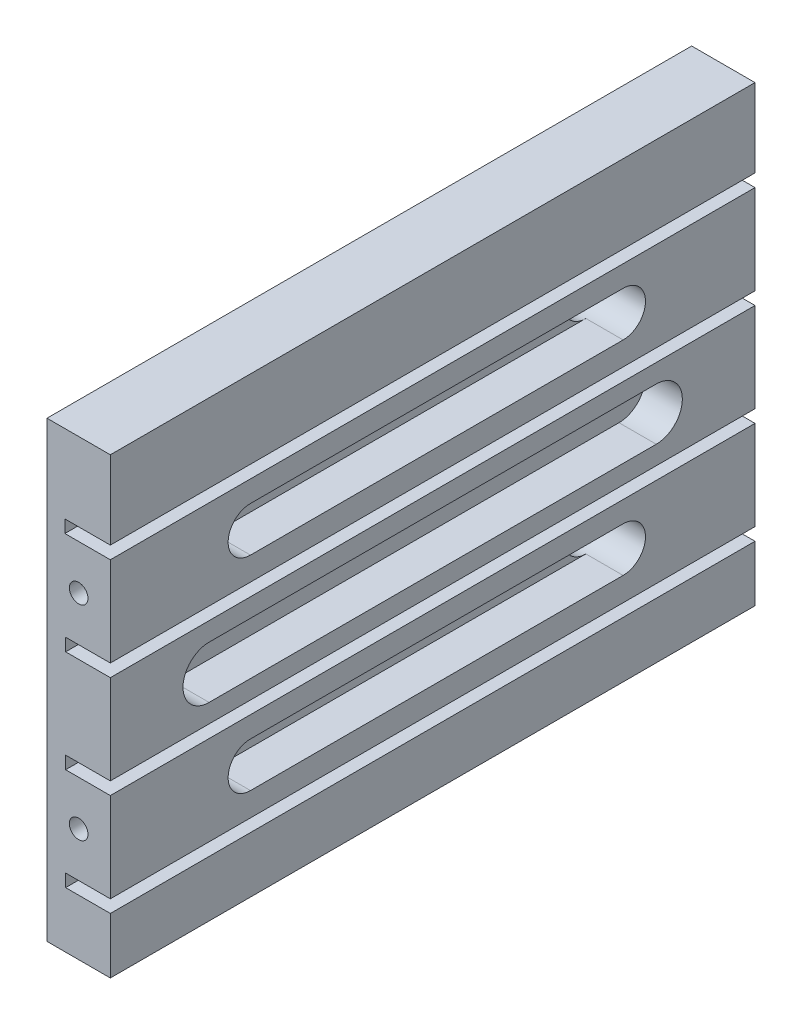
SolidWorks part; units mm, degrees
material "6061-T6 (SS)"
ref_plane "Front Plane" through (0, 0, 0) normal (0, 0, 1) x (1, 0, 0)
ref_plane "Top Plane" through (0, 0, 0) normal (0, 1, 0) x (1, 0, 0)
ref_plane "Right Plane" through (0, 0, 0) normal (1, 0, 0) x (0, 0, -1)
sketch "Sketch1" plane through (0, 0, 0) normal (0, 0, 1) x (1, 0, 0)
  line L0 (0, 0) -> (0, 60.8)
  line L1 (0, 60.8) -> (8.5, 60.8)
  line L2 (8.5, 60.8) -> (8.5, 50.3)
  line L3 (8.5, 50.3) -> (2.4, 50.3)
  line L4 (2.4, 50.3) -> (2.4, 48.6)
  line L5 (2.4, 48.6) -> (8.5, 48.6)
  line L6 (8.5, 48.6) -> (8.5, 36.6)
  line L7 (8.5, 36.6) -> (2.5, 36.6)
  line L8 (2.5, 36.6) -> (2.5, 34.9)
  line L9 (2.5, 34.9) -> (8.5, 34.9)
  line L10 (8.5, 34.9) -> (8.5, 22.9)
  line L11 (8.5, 22.9) -> (2.5, 22.9)
  line L12 (2.5, 22.9) -> (2.5, 21.2)
  line L13 (2.5, 21.2) -> (8.5, 21.2)
  line L14 (8.5, 21.2) -> (8.5, 9.2)
  line L15 (8.5, 9.2) -> (2.5, 9.2)
  line L16 (2.5, 9.2) -> (2.5, 7.5)
  line L17 (2.5, 7.5) -> (8.5, 7.5)
  line L18 (8.5, 7.5) -> (8.5, 0)
  line L19 (8.5, 0) -> (0, 0)
  dimension "D1" = 60.8
  dimension "D2" = 8.5
  dimension "D3" = 10.5
  dimension "D4" = 1.7
  dimension "D5" = 6.1
  dimension "D6" = 12
  dimension "D7" = 1.7
  dimension "D8" = 12
  dimension "D9" = 12
  dimension "D10" = 1.7
  dimension "D11" = 1.7
  dimension "D12" = 2.5
  dimension "D13" = 2.5
  dimension "D14" = 2.5
  dimension "D15" = 8.5
  dimension "D16" = 8.5
  dimension "D17" = 8.5
  dimension "D18" = 8.5
extrude "Boss-Extrude1" add sketch "Sketch1" along normal blind 86.5
sketch "Sketch2" plane through (0, 0, 86.5) normal (0, 0, 1) x (1, 0, 0)
  line L0 (8.5, 36.6) -> (8.5, 48.6) construction
  line L3 (8.5, 48.6) -> (2.4, 48.6) construction
  line L4 (8.5, 21.2) -> (2.5, 21.2) construction
  line L8 (8.5, 9.2) -> (8.5, 21.2) construction
  point P0 (4.25, 15.2)
  point P11 (4.25, 42.6)
  dimension "D1" = 4.25
  dimension "D2" = 6
  dimension "D3" = 4.25
  dimension "D4" = 6
hole_wizard "M3x0.5 Tapped Hole2" positions "Sketch3" profile "Sketch4" tap size "M3x0.5" standard "ANSI Metric"
sketch "Sketch3" plane through (0, 0, 86.5) normal (0, 0, 1) x (1, 0, 0)
  point P0 (4.25, 42.6)
  point P3 (4.25, 15.2)
sketch "Sketch4" plane through (4.25, 42.6, 86.5) normal (1, 0, 0) x (0, -1, 0)
  line L0 (0, 0) -> (0, 6.7511)
  line L1 (0, 6.7511) -> (1.25, 6)
  line L2 (1.25, 6) -> (1.25, 0)
  line L5 (1.25, 0) -> (0, 0)
  line L10 (0, 6.7511) -> (-1.25, 6) construction
  line L11 (0, -6.35) -> (0, 107.95) construction
  dimension "Tap Drill Dia." = 2.5
  dimension "Tap Drill Depth" = 6
  dimension "Drill Angle" = 118
ref_plane "Plane1" through (0, 0, 43.25) normal (0, 0, 1) x (1, 0, 0)
mirror "Mirror1" about plane through (0, 0, 43.25) normal (0, 0, 1) of "M3x0.5 Tapped Hole2"
sketch "Sketch5" plane through (0, 0, 0) normal (-1, 0, 0) x (0, 0, 1)
  line L1 (86.5, 60.8) -> (0, 60.8) construction
  line L5 (0, 60.8) -> (0, 0) construction
  line L7 (86.5, 0) -> (0, 0) construction
  line L8 (86.5, 60.8) -> (86.5, 0) construction
  point P0 (78.25, 5)
  point P3 (8.25, 5)
  point P4 (8.25, 55.8)
  point P7 (78.25, 55.8)
  dimension "D1" = 5
  dimension "D2" = 8.25
  dimension "D3" = 70
  dimension "D4" = 5
  dimension "D5" = 5
  dimension "D6" = 8.25
  dimension "D7" = 8.25
  dimension "D8" = 5
hole_wizard "M3x0.5 Tapped Hole1" positions "Sketch10" profile "Sketch11" tap size "M3x0.5" standard "ANSI Metric"
sketch "Sketch10" plane through (0, 0, 0) normal (-1, 0, 0) x (0, 0, 1)
  line L0 (43.25, 60.8) -> (43.25, 0) construction
  line L1 (86.5, 60.8) -> (0, 60.8) construction
  line L2 (86.5, 0) -> (0, 0) construction
  line L7 (43.25, 54) -> (8.25, 54) construction
  line L12 (43.25, 5) -> (8.25, 5) construction
  point P16 (8.25, 54)
  point P26 (8.25, 5)
  dimension "D1" = 49
sketch "Sketch11" plane through (0, 5, 8.25) normal (0, 1, 0) x (0, 0, 1)
  line L0 (0, 0) -> (0, 4.7511)
  line L1 (0, 4.7511) -> (1.25, 4)
  line L2 (1.25, 4) -> (1.25, 0)
  line L5 (1.25, 0) -> (0, 0)
  line L10 (0, 4.7511) -> (-1.25, 4) construction
  line L11 (0, -6.35) -> (0, 107.95) construction
  dimension "Tap Drill Dia." = 2.5
  dimension "Tap Drill Depth" = 4
  dimension "Drill Angle" = 118
ref_plane "Plane2" through (0, 0, 43.25) normal (0, 0, -1) x (-1, 0, 0)
mirror "Mirror2" about plane through (0, 0, 43.25) normal (0, 0, -1) of "M3x0.5 Tapped Hole1"
sketch "Sketch14" plane through (8.5, 0, 0) normal (1, 0, 0) x (0, 0, -1)
  line L0 (-43.25, 60.8) -> (-43.25, 0) construction
  line L1 (-86.5, 60.8) -> (0, 60.8) construction
  line L2 (-86.5, 0) -> (0, 0) construction
  line L3 (-86.5, 28.9) -> (0, 28.9) construction
  line L4 (-86.5, 22.9) -> (-86.5, 34.9) construction
  line L5 (0, 22.9) -> (0, 34.9) construction
  line L6 (-73.25, 32.4) -> (-13.25, 32.4)
  line L7 (-13.25, 25.4) -> (-73.25, 25.4)
  circle A0 centre (-73.25, 28.9) radius 3.5
  circle A1 centre (-13.25, 28.9) radius 3.5
  dimension "D1" = 7
  dimension "D2" = 30
extrude "Cut-Extrude3" cut sketch "Sketch14" against normal offset from surface (5 mm away) 5 contours A1 L6 A0 L7 | A0 | A1 up to face at (8.5, 28.9, 43.25)
sketch "Sketch12" plane through (8.5, 0, 0) normal (1, 0, 0) x (0, 0, -1)
  line L0 (-42.6954, 60.8) -> (-42.6954, 0) construction
  line L1 (-86.5, 60.8) -> (0, 60.8) construction
  line L2 (-86.5, 0) -> (0, 0) construction
  line L4 (-67.6954, 45.7404) -> (-17.6954, 45.7404)
  line L5 (-67.6954, 39.7404) -> (-17.6954, 39.7404)
  line L6 (-67.6954, 18.3789) -> (-17.6954, 18.3789)
  line L7 (-67.6954, 12.3789) -> (-17.6954, 12.3789)
  circle A0 centre (-67.6954, 42.7404) radius 3
  circle A1 centre (-17.6954, 42.7404) radius 3
  circle A2 centre (-17.6954, 15.3789) radius 3
  circle A3 centre (-67.6954, 15.3789) radius 3
  dimension "D1" = 6
  dimension "D2" = 25
extrude "Cut-Extrude1" cut sketch "Sketch12" against normal offset from surface (5 mm away) 5 contours A0 | A3 | A2 | A1 | L0 L6 A3 L7 | L6 L0 L7 A2 | L4 L0 L5 A1 | L0 L4 A0 L5
sketch "Sketch13" plane through (3.5, 0, 0) normal (1, 0, 0) x (0, 0, -1)
  circle A0 centre (-67.6954, 42.7404) radius 3
  circle A1 centre (-17.6954, 42.7404) radius 3
  circle A2 centre (-17.6954, 15.3789) radius 3
  circle A3 centre (-67.6954, 15.3789) radius 3
extrude "Cut-Extrude2" cut sketch "Sketch13" against normal through all
